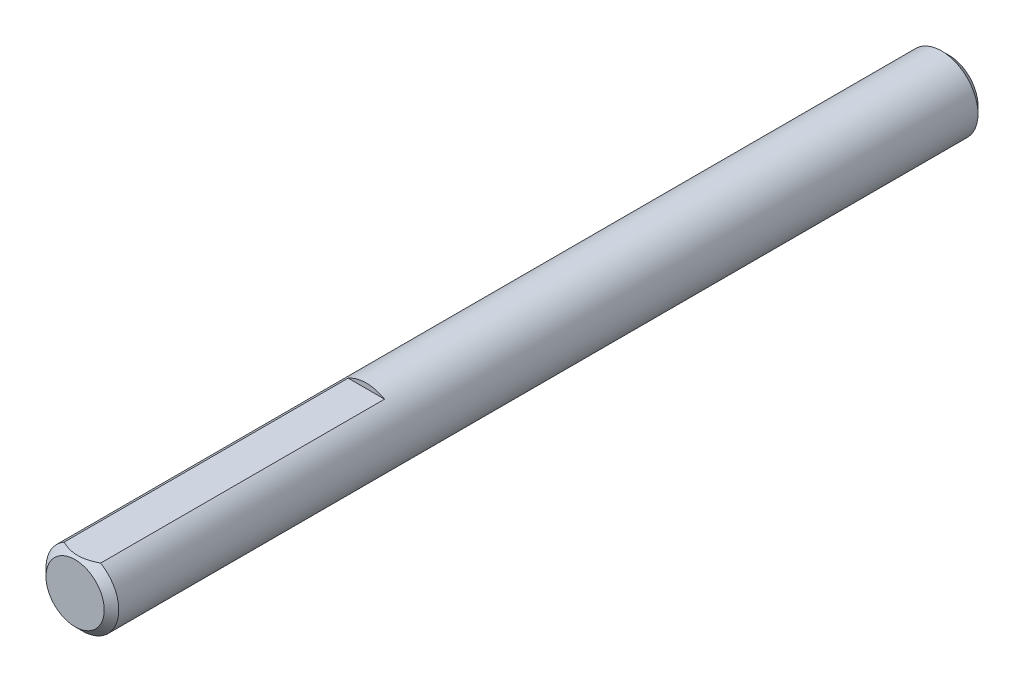
SolidWorks part; units mm, degrees
ref_plane "Front" through (0, 0, 0) normal (0, 0, 1) x (1, 0, 0)
ref_plane "Top" through (0, 0, 0) normal (0, 1, 0) x (1, 0, 0)
ref_plane "Right" through (0, 0, 0) normal (1, 0, 0) x (0, 0, -1)
sketch "Sketch1" plane through (0, 0, 0) normal (0, 0, 1) x (1, 0, 0)
  circle A0 centre (0, 0) radius 3.175
  dimension "D1" = 6.35
extrude "Extrude1" add sketch "Sketch1" along normal mid plane 76.2
chamfer "Chamfer1" distance 0.635 angle 45 2 edges at (3.175, 0, -38.1) (3.175, 0, 38.1)
ref_plane "Plane1" through (0, 0, 12.7) normal (0, 0, 1) x (1, 0, 0)
sketch "Sketch13" plane through (0, 0, 12.7) normal (0, 0, 1) x (1, 0, 0)
  line L3 (-1.5875, 2.7496) -> (1.5875, 2.7496)
  circle A0 centre (0, 0) radius 3.175 construction
  arc A1 (1.5875, 2.7496) -> (-1.5875, 2.7496) centre (0, 0) ccw
  dimension "D1" = 3.175
extrude "Extrude7" cut sketch "Sketch13" along normal through all
equation "\"D1@Chamfer1\" = \"D1@Sketch1\" * .1"
equation "\"D1@Sketch13\" = \"D1@Sketch1\" * .5"
